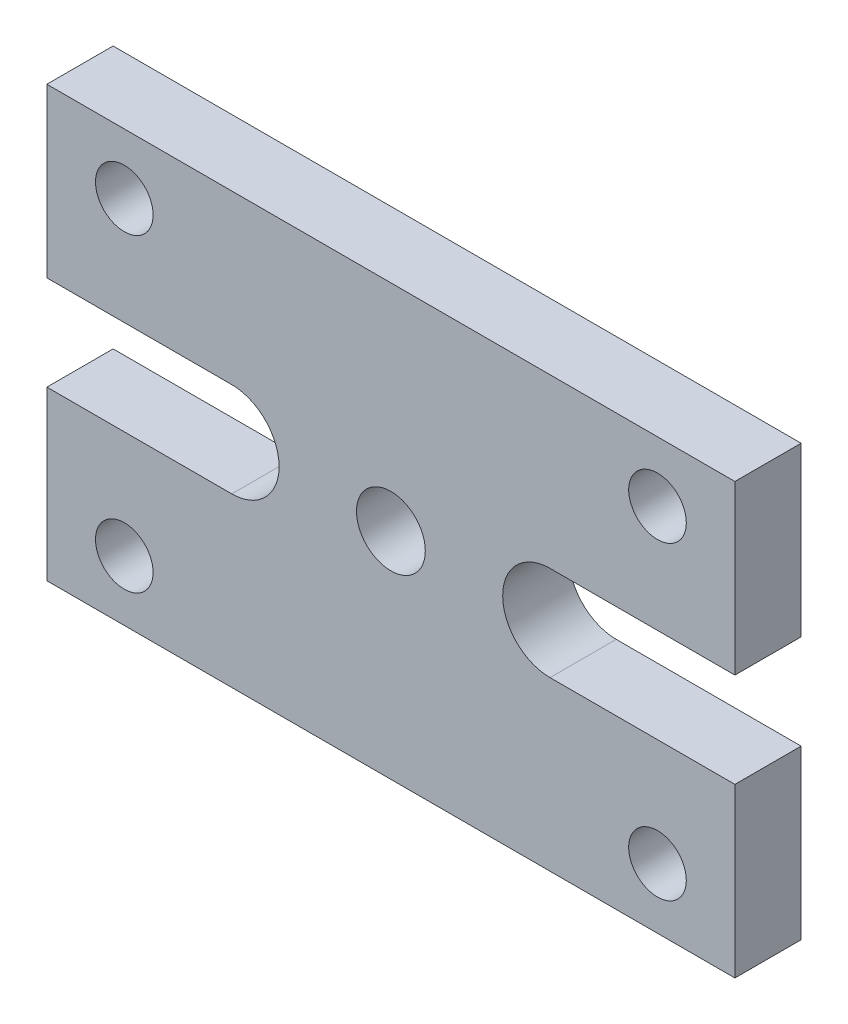
SolidWorks part; units mm, degrees
material "304 SSTL"
ref_plane "Front" through (0, 0, 0) normal (0, 0, 1) x (1, 0, 0)
ref_plane "Top" through (0, 0, 0) normal (0, 1, 0) x (1, 0, 0)
ref_plane "Right" through (0, 0, 0) normal (1, 0, 0) x (0, 0, -1)
sketch "Sketch1" plane through (0, 0, 0) normal (0, 0, 1) x (1, 0, 0)
  line L0 (0, 0) -> (0, 25) construction
  line L1 (-40, 25) -> (40, 25)
  line L2 (-40, 25) -> (-40, 5.5)
  line L3 (-40, -25) -> (40, -25)
  line L4 (40, 25) -> (40, 5.5)
  line L5 (0, 0) -> (-18.5, 0) construction
  line L6 (0, 0) -> (18.5, 0) construction
  line L7 (-18.5, 5.5) -> (-40, 5.5)
  line L8 (-18.5, -5.5) -> (-40, -5.5)
  line L9 (18.5, 5.5) -> (40, 5.5)
  line L10 (18.5, -5.5) -> (40, -5.5)
  line L11 (-40, -5.5) -> (-40, -25)
  line L12 (40, -5.5) -> (40, -25)
  arc A0 (-18.5, -5.5) -> (-18.5, 5.5) centre (-18.5, 0) ccw
  arc A1 (18.5, 5.5) -> (18.5, -5.5) centre (18.5, 0) ccw
  dimension "D1" = 80
  dimension "D2" = 18.5
  dimension "D3" = 25
  dimension "D4" = 25
  dimension "D5" = 11
extrude "Boss-Extrude1" add sketch "Sketch1" along normal blind 7.7
hole_wizard "Ø6.7 (6.7) Diameter Hole1" positions "Sketch3" profile "Sketch4" hole size "Ø6.7" standard "Ansi Metric" end condition through all
sketch "Sketch3" plane through (0, 0, 7.7) normal (0, 0, 1) x (1, 0, 0)
  line L0 (-31, 18) -> (31, 18) construction
  line L1 (-31, 18) -> (-31, -18) construction
  line L2 (-31, -18) -> (31, -18) construction
  line L3 (31, -18) -> (31, 18) construction
  line L5 (0, 0) -> (0, 18) construction
  line L6 (0, 0) -> (31, 0) construction
  point P0 (31, 18)
  point P1 (-31, 18)
  point P3 (-31, -18)
  point P5 (31, -18)
  dimension "D1" = 36
  dimension "D2" = 62
sketch "Sketch4" plane through (31, 18, 7.7) normal (1, 0, 0) x (0, -1, 0)
  line L0 (0, 0) -> (0, 7.7)
  line L1 (0, 7.7) -> (3.35, 7.7)
  line L2 (3.35, 7.7) -> (3.35, 0)
  line L5 (3.35, 0) -> (0, 0)
  line L11 (0, -6.35) -> (0, 107.95) construction
  dimension "Thru Hole Dia." = 6.7
  dimension "Thru Hole Depth" = 7.7
hole_wizard "Ø8.0 (8) Diameter Hole1" positions "Sketch6" profile "Sketch7" hole size "Ø8.0" standard "Ansi Metric" end condition through all
sketch "Sketch6" plane through (0, 0, 7.7) normal (0, 0, 1) x (1, 0, 0)
  point P0 (0, 0)
sketch "Sketch7" plane through (0, 0, 7.7) normal (1, 0, 0) x (0, -1, 0)
  line L0 (0, 0) -> (0, 7.7)
  line L1 (0, 7.7) -> (4, 7.7)
  line L2 (4, 7.7) -> (4, 0)
  line L5 (4, 0) -> (0, 0)
  line L11 (0, -6.35) -> (0, 107.95) construction
  dimension "Thru Hole Dia." = 8
  dimension "Thru Hole Depth" = 7.7
